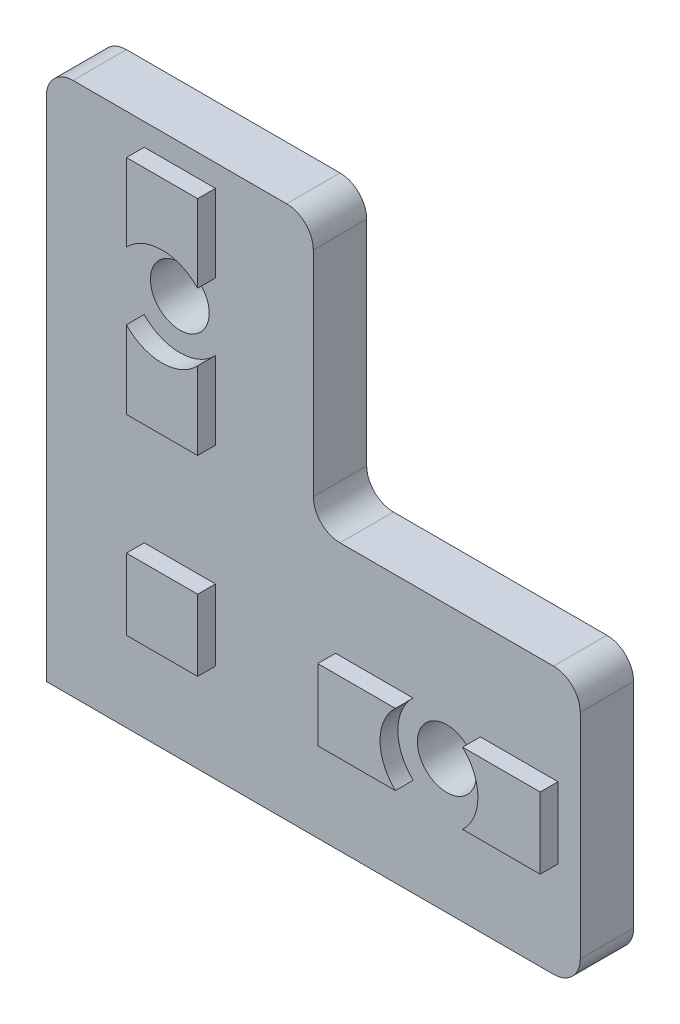
SolidWorks part; units mm, degrees
ref_plane "Přední rovina" through (0, 0, 0) normal (0, 0, 1) x (1, 0, 0)
ref_plane "Horní rovina" through (0, 0, 0) normal (0, 1, 0) x (1, 0, 0)
ref_plane "Pravá rovina" through (0, 0, 0) normal (1, 0, 0) x (0, 0, -1)
sketch "Skica1" plane through (0, 0, 0) normal (0, 0, 1) x (1, 0, 0)
  line L0 (0, 0) -> (57, 0)
  line L1 (60, 3) -> (60, 27)
  line L2 (57, 30) -> (33, 30)
  line L3 (30, 33) -> (30, 57)
  line L4 (27, 60) -> (3, 60)
  line L5 (0, 57) -> (0, 0)
  arc A0 (57, 0) -> (60, 3) centre (57, 3) ccw
  arc A1 (60, 27) -> (57, 30) centre (57, 27) ccw
  arc A2 (33, 30) -> (30, 33) centre (33, 33) cw
  arc A3 (30, 57) -> (27, 60) centre (27, 57) ccw
  arc A4 (3, 60) -> (0, 57) centre (3, 57) ccw
  point P15 (30, 60)
  point P18 (0, 60)
  dimension "D3" = 3
  dimension "D1" = 30
  dimension "D2" = 60
extrude "Přidat vysunutím1" add sketch "Skica1" along normal blind 6
sketch "Skica2" plane through (0, 0, 6) normal (0, 0, 1) x (1, 0, 0)
  line L0 (60, 15) -> (0, 15)
  line L1 (60, 3) -> (60, 27) construction
  line L2 (0, 57) -> (0, 0) construction
  line L3 (15, 60) -> (15, 0)
  line L4 (27, 60) -> (3, 60) construction
  line L5 (0, 0) -> (57, 0) construction
  point P12 (45, 15)
  point P13 (15, 45)
  dimension "D1" = 15
  dimension "D2" = 15
hole_wizard "M6 díra s vůlí1" positions "Skica3" profile "Skica4" hole size "M6" standard "ANSI Metric" end condition through all
sketch "Skica3" plane through (0, 0, 6) normal (0, 0, 1) x (1, 0, 0)
  point P0 (45, 15)
  point P3 (15, 45)
sketch "Skica4" plane through (45, 15, 6) normal (1, 0, 0) x (0, -1, 0)
  line L0 (0, 0) -> (0, 6)
  line L1 (0, 6) -> (3.3, 6)
  line L2 (3.3, 6) -> (3.3, 0)
  line L5 (3.3, 0) -> (0, 0)
  line L11 (0, -6.35) -> (0, 107.95) construction
  dimension "Průměr díry skrz" = 6.6
  dimension "Hloubka díry skrz" = 6
sketch "Skica5" plane through (0, 0, 6) normal (0, 0, 1) x (1, 0, 0)
  line L1 (32.5, 19) -> (57.5, 19)
  line L2 (32.5, 19) -> (32.5, 11)
  line L3 (32.5, 11) -> (57.5, 11)
  line L4 (57.5, 19) -> (57.5, 11)
  line L5 (32.5, 19) -> (57.5, 11) construction
  line L6 (32.5, 11) -> (57.5, 19) construction
  line L7 (11, 57.5) -> (19, 57.5)
  line L8 (11, 57.5) -> (11, 32.5)
  line L9 (11, 32.5) -> (19, 32.5)
  line L10 (19, 57.5) -> (19, 32.5)
  line L11 (11, 57.5) -> (19, 32.5) construction
  line L12 (11, 32.5) -> (19, 57.5) construction
  line L13 (11, 19) -> (19, 19)
  line L14 (11, 19) -> (11, 11)
  line L15 (11, 11) -> (19, 11)
  line L16 (19, 19) -> (19, 11)
  line L17 (11, 19) -> (19, 11) construction
  line L18 (11, 11) -> (19, 19) construction
  circle A0 centre (15, 45) radius 5.5
  circle A1 centre (45, 15) radius 5.5
  point P0 (45, 15)
  point P6 (15, 45)
  point P12 (15, 15)
  point P13 (15, 15)
  point P15 (15, 15)
  dimension "D7" = 11
  dimension "D1" = 8
  dimension "D2" = 8
  dimension "D3" = 25
  dimension "D4" = 25
  dimension "D5" = 15
  dimension "D6" = 8
extrude "Přidat vysunutím2" add sketch "Skica5" along normal blind 2 contours A0 L8 L9 L10 | A0 L10 L7 L8 | A1 L1 L2 L3 | A1 L3 L4 L1 | L16 L13 L14 L15
